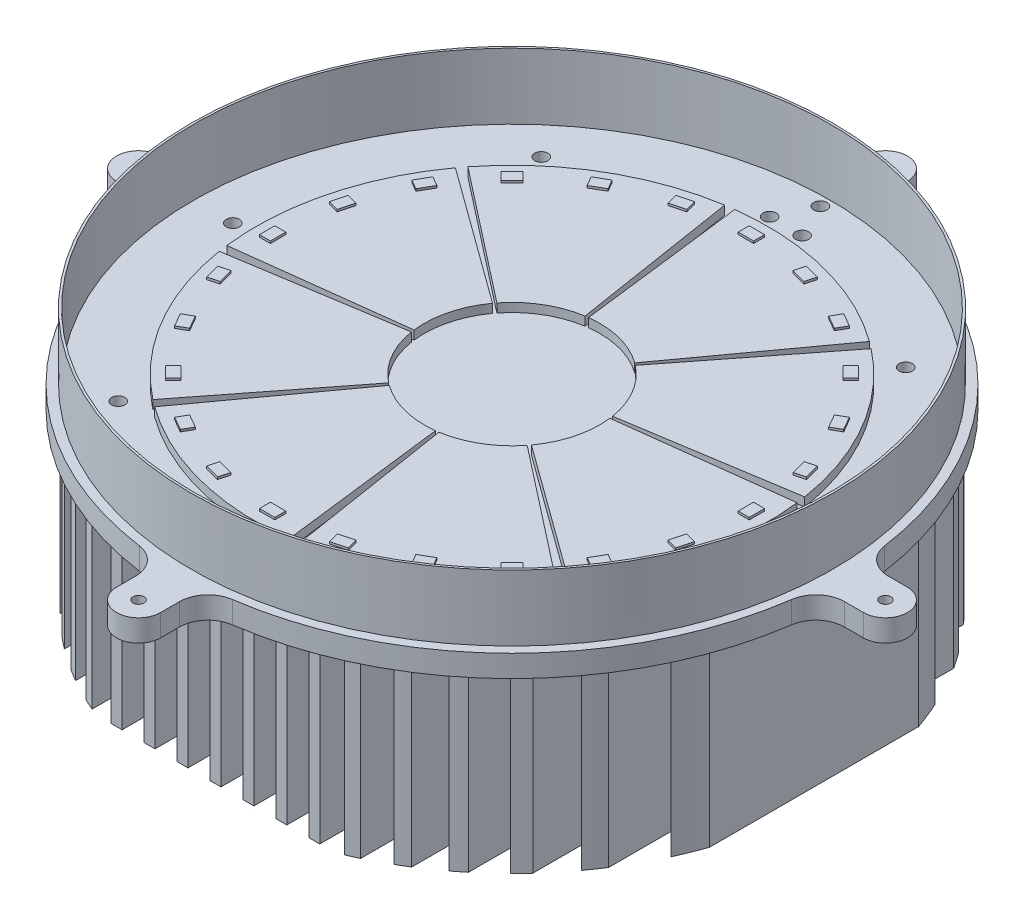
SolidWorks part; units mm, degrees
ref_plane "Front Plane" through (0, 0, 0) normal (0, 0, 1) x (1, 0, 0)
ref_plane "Top Plane" through (0, 0, 0) normal (0, 1, 0) x (1, 0, 0)
ref_plane "Right Plane" through (0, 0, 0) normal (1, 0, 0) x (0, 0, -1)
sketch "Sketch2" plane through (0, 0, 0) normal (0, 1, 0) x (1, 0, 0)
  line L0 (0, 0) -> (0, -224.3017) construction
  line L1 (0, 0) -> (0, 200) construction
  line L2 (0, 0) -> (207.2583, 0) construction
  line L3 (0, 0) -> (-200, 0) construction
  circle A0 centre (0, 0) radius 146
  circle A1 centre (0, 0) radius 145
  point P36 (0, 0)
  dimension "D1" = 290
  dimension "D2" = 292
extrude "Boss-Extrude2" add sketch "Sketch2" along normal blind 30 contours A1 | A0
sketch "Sketch3" plane through (0, 0, 0) normal (0, 1, 0) x (1, 0, 0)
  line L0 (0, 0) -> (211.9111, 0) construction
  line L1 (0, 0) -> (-205.2426, 0) construction
  line L2 (0, 0) -> (0, 170) construction
  line L3 (0, 0) -> (0, -200) construction
  line L4 (161.3691, 10) -> (170, 10)
  line L5 (161.3691, -10) -> (170, -10)
  line L6 (-10, 161.3691) -> (-10, 170)
  line L7 (10, 161.3691) -> (10, 170)
  line L8 (10, -161.3691) -> (10, -170)
  line L9 (-10, -161.3691) -> (-10, -170)
  line L10 (-161.3691, -10) -> (-170, -10)
  line L11 (-161.3691, 10) -> (-170, 10)
  arc A0 (-21.1656, 148.4992) -> (-148.4992, 21.1656) centre (0, 0) ccw
  circle A1 centre (0, 170) radius 2.5
  arc A2 (-10, 170) -> (10, 170) centre (0, 170) cw
  arc A3 (10, 161.3691) -> (21.1656, 148.4992) centre (23, 161.3691) ccw
  arc A4 (-10, 161.3691) -> (-21.1656, 148.4992) centre (-23, 161.3691) cw
  arc A5 (170, 10) -> (170, -10) centre (170, 0) cw
  arc A6 (161.3691, 10) -> (148.4992, 21.1656) centre (161.3691, 23) cw
  circle A7 centre (170, 0) radius 2.5
  arc A8 (161.3691, -10) -> (148.4992, -21.1656) centre (161.3691, -23) ccw
  arc A9 (10, -170) -> (-10, -170) centre (0, -170) cw
  arc A10 (10, -161.3691) -> (21.1656, -148.4992) centre (23, -161.3691) cw
  circle A11 centre (0, -170) radius 2.5
  arc A12 (-10, -161.3691) -> (-21.1656, -148.4992) centre (-23, -161.3691) ccw
  arc A13 (-170, -10) -> (-170, 10) centre (-170, 0) cw
  arc A14 (-161.3691, -10) -> (-148.4992, -21.1656) centre (-161.3691, -23) cw
  circle A15 centre (-170, 0) radius 2.5
  arc A16 (-161.3691, 10) -> (-148.4992, 21.1656) centre (-161.3691, 23) ccw
  arc A17 (-148.4992, -21.1656) -> (-21.1656, -148.4992) centre (0, 0) ccw
  arc A18 (148.4992, 21.1656) -> (21.1656, 148.4992) centre (0, 0) ccw
  arc A19 (21.1656, -148.4992) -> (148.4992, -21.1656) centre (0, 0) ccw
  point P53 (0, 0)
  dimension "D1" = 300
  dimension "D4" = 5
  dimension "D2" = 4
extrude "Boss-Extrude4" add sketch "Sketch3" against normal blind 10
sketch "Sketch4" plane through (0, -10, 0) normal (0, -1, 0) x (1, 0, 0)
  line L0 (0, 0) -> (0, -192.7937) construction
  line L1 (0, 0) -> (0, 216.5128) construction
  line L2 (0, 0) -> (-235.9747, 0) construction
  line L3 (0, 0) -> (242.3846, 0) construction
  line L4 (2.5, -135) -> (-2.5, -135)
  line L5 (2.5, 135) -> (-2.5, 135)
  line L6 (-2.5, -135) -> (-2.5, 135)
  line L7 (2.5, -135) -> (2.5, 135)
  line L8 (12.5, -135) -> (12.5, 135)
  line L9 (17.5, -135) -> (12.5, -135)
  line L10 (17.5, -135) -> (17.5, 135)
  line L11 (17.5, 135) -> (12.5, 135)
  line L12 (27.5, -135) -> (27.5, 135)
  line L13 (32.5, -135) -> (27.5, -135)
  line L14 (32.5, -135) -> (32.5, 135)
  line L15 (32.5, 135) -> (27.5, 135)
  line L16 (42.5, -135) -> (42.5, 135)
  line L17 (47.5, -135) -> (42.5, -135)
  line L18 (47.5, -135) -> (47.5, 135)
  line L19 (47.5, 135) -> (42.5, 135)
  line L20 (57.5, -133.6563) -> (57.5, 133.6563)
  line L22 (62.5, -131.3925) -> (62.5, 131.3925)
  line L24 (72.5, -126.1507) -> (72.5, 126.1507)
  line L26 (77.5, -123.1422) -> (77.5, 123.1422)
  line L28 (87.5, -116.2497) -> (87.5, 116.2497)
  line L30 (92.5, -112.3121) -> (92.5, 112.3121)
  line L32 (102.5, -103.2666) -> (102.5, 103.2666)
  line L34 (107.5, -98.051) -> (107.5, 98.051)
  line L36 (117.5, -85.8138) -> (117.5, 85.8138)
  line L38 (122.5, -78.5111) -> (122.5, 78.5111)
  line L40 (132.5, -60.1166) -> (132.5, 60.1166)
  line L42 (137.5, -47.5815) -> (137.5, 47.5815)
  line L44 (-12.5, -135) -> (-17.5, -135)
  line L45 (-12.5, -135) -> (-12.5, 135)
  line L46 (-17.5, -135) -> (-17.5, 135)
  line L47 (-12.5, 135) -> (-17.5, 135)
  line L48 (-27.5, -135) -> (-32.5, -135)
  line L49 (-27.5, -135) -> (-27.5, 135)
  line L50 (-32.5, -135) -> (-32.5, 135)
  line L51 (-27.5, 135) -> (-32.5, 135)
  line L52 (-42.5, -135) -> (-47.5, -135)
  line L53 (-42.5, -135) -> (-42.5, 135)
  line L54 (-47.5, -135) -> (-47.5, 135)
  line L55 (-42.5, 135) -> (-47.5, 135)
  line L57 (-57.5, -133.6563) -> (-57.5, 133.6563)
  line L58 (-62.5, -131.3925) -> (-62.5, 131.3925)
  line L61 (-72.5, -126.1507) -> (-72.5, 126.1507)
  line L62 (-77.5, -123.1422) -> (-77.5, 123.1422)
  line L65 (-87.5, -116.2497) -> (-87.5, 116.2497)
  line L66 (-92.5, -112.3121) -> (-92.5, 112.3121)
  line L69 (-102.5, -103.2666) -> (-102.5, 103.2666)
  line L70 (-107.5, -98.051) -> (-107.5, 98.051)
  line L73 (-117.5, -85.8138) -> (-117.5, 85.8138)
  line L74 (-122.5, -78.5111) -> (-122.5, 78.5111)
  line L77 (-132.5, -60.1166) -> (-132.5, 60.1166)
  line L78 (-137.5, -47.5815) -> (-137.5, 47.5815)
  line L80 (2.5, -135) -> (-12.5, -135) construction
  line L81 (62.5, 135) -> (57.5, 135) [skipped]
  line L82 (77.5, 135) -> (72.5, 135) [skipped]
  line L83 (92.5, 135) -> (87.5, 135) [skipped]
  line L84 (107.5, 135) -> (102.5, 135) [skipped]
  line L85 (137.5, 135) -> (132.5, 135) [skipped]
  line L86 (122.5, 135) -> (117.5, 135) [skipped]
  line L87 (-57.5, 135) -> (-62.5, 135) [skipped]
  line L88 (-72.5, 135) -> (-77.5, 135) [skipped]
  line L89 (-87.5, 135) -> (-92.5, 135) [skipped]
  line L90 (-102.5, 135) -> (-107.5, 135) [skipped]
  line L91 (-117.5, 135) -> (-122.5, 135) [skipped]
  line L92 (-132.5, 135) -> (-137.5, 135) [skipped]
  line L93 (-57.5, -135) -> (-62.5, -135) [skipped]
  line L94 (62.5, -135) -> (57.5, -135) [skipped]
  line L95 (77.5, -135) -> (72.5, -135) [skipped]
  line L96 (137.5, -135) -> (132.5, -135) [skipped]
  line L97 (122.5, -135) -> (117.5, -135) [skipped]
  line L98 (107.5, -135) -> (102.5, -135) [skipped]
  line L99 (92.5, -135) -> (87.5, -135) [skipped]
  line L100 (-132.5, -135) -> (-137.5, -135) [skipped]
  line L101 (-117.5, -135) -> (-122.5, -135) [skipped]
  line L102 (-102.5, -135) -> (-107.5, -135) [skipped]
  line L103 (-87.5, -135) -> (-92.5, -135) [skipped]
  line L104 (-72.5, -135) -> (-77.5, -135) [skipped]
  arc A2 (132.5, -60.1166) -> (137.5, -47.5815) centre (0, 0) ccw
  arc A3 (117.5, -85.8138) -> (122.5, -78.5111) centre (0, 0) ccw
  arc A4 (102.5, -103.2666) -> (107.5, -98.051) centre (0, 0) ccw
  arc A5 (87.5, -116.2497) -> (92.5, -112.3121) centre (0, 0) ccw
  arc A6 (72.5, -126.1507) -> (77.5, -123.1422) centre (0, 0) ccw
  arc A7 (57.5, -133.6563) -> (62.5, -131.3925) centre (0, 0) ccw
  arc A8 (-77.5, -123.1422) -> (-72.5, -126.1507) centre (0, 0) ccw
  arc A9 (-62.5, -131.3925) -> (-57.5, -133.6563) centre (0, 0) ccw
  arc A10 (-92.5, -112.3121) -> (-87.5, -116.2497) centre (0, 0) ccw
  arc A11 (-107.5, -98.051) -> (-102.5, -103.2666) centre (0, 0) ccw
  arc A12 (-122.5, -78.5111) -> (-117.5, -85.8138) centre (0, 0) ccw
  arc A13 (-137.5, -47.5815) -> (-132.5, -60.1166) centre (0, 0) ccw
  arc A14 (137.5, 47.5815) -> (132.5, 60.1166) centre (0, 0) ccw
  arc A15 (122.5, 78.5111) -> (117.5, 85.8138) centre (0, 0) ccw
  arc A16 (107.5, 98.051) -> (102.5, 103.2666) centre (0, 0) ccw
  arc A17 (92.5, 112.3121) -> (87.5, 116.2497) centre (0, 0) ccw
  arc A18 (77.5, 123.1422) -> (72.5, 126.1507) centre (0, 0) ccw
  arc A19 (62.5, 131.3925) -> (57.5, 133.6563) centre (0, 0) ccw
  arc A20 (-57.5, 133.6563) -> (-62.5, 131.3925) centre (0, 0) ccw
  arc A21 (-72.5, 126.1507) -> (-77.5, 123.1422) centre (0, 0) ccw
  arc A22 (-87.5, 116.2497) -> (-92.5, 112.3121) centre (0, 0) ccw
  arc A23 (-102.5, 103.2666) -> (-107.5, 98.051) centre (0, 0) ccw
  arc A24 (-117.5, 85.8138) -> (-122.5, 78.5111) centre (0, 0) ccw
  arc A25 (-132.5, 60.1166) -> (-137.5, 47.5815) centre (0, 0) ccw
  dimension "D5" = 291
  dimension "D1" = 135
  dimension "D2" = 2.5
  dimension "D4" = 15
  dimension "D3" = 10
extrude "Boss-Extrude5" add sketch "Sketch4" along normal blind 80
sketch "Sketch8" plane through (0, 0, 0) normal (0, 1, 0) x (1, 0, 0)
  line L8 (4.8748, -39.7018) -> (14.1944, -115.6039)
  line L9 (-24.6265, -31.5204) -> (-71.7074, -91.7813)
  line L10 (-39.7018, -4.8748) -> (-115.6039, -14.1944)
  line L11 (-31.5204, 24.6265) -> (-91.7813, 71.7074)
  line L12 (-4.8748, 39.7018) -> (-14.1944, 115.6039)
  line L13 (24.6265, 31.5204) -> (71.7074, 91.7813)
  line L14 (39.7018, 4.8748) -> (115.6039, 14.1944)
  line L15 (31.5204, -24.6265) -> (91.7813, -71.7074)
  line L16 (6.2574, -39.5075) -> (18.2202, -115.0381)
  line L17 (32.3607, -23.5114) -> (94.2279, -68.4606)
  line L18 (39.5075, 6.2574) -> (115.0381, 18.2202)
  line L19 (23.5114, 32.3607) -> (68.4606, 94.2279)
  line L20 (-6.2574, 39.5075) -> (-18.2202, 115.0381)
  line L21 (-32.3607, 23.5114) -> (-94.2279, 68.4606)
  line L22 (-39.5075, -6.2574) -> (-115.0381, -18.2202)
  line L23 (-23.5114, -32.3607) -> (-68.4606, -94.2279)
  arc A0 (115.0381, 18.2202) -> (71.7074, 91.7813) centre (0, 0) ccw
  arc A1 (32.3607, -23.5114) -> (39.7018, 4.8748) centre (0, 0) ccw
  arc A2 (6.2574, -39.5075) -> (31.5204, -24.6265) centre (0, 0) ccw
  arc A3 (-23.5114, -32.3607) -> (4.8748, -39.7018) centre (0, 0) ccw
  arc A4 (-39.5075, -6.2574) -> (-24.6265, -31.5204) centre (0, 0) ccw
  arc A5 (-32.3607, 23.5114) -> (-39.7018, -4.8748) centre (0, 0) ccw
  arc A6 (-6.2574, 39.5075) -> (-31.5204, 24.6265) centre (0, 0) ccw
  arc A7 (23.5114, 32.3607) -> (-4.8748, 39.7018) centre (0, 0) ccw
  arc A8 (39.5075, 6.2574) -> (24.6265, 31.5204) centre (0, 0) ccw
  arc A9 (94.2279, -68.4606) -> (115.6039, 14.1944) centre (0, 0) ccw
  arc A10 (18.2202, -115.0381) -> (91.7813, -71.7074) centre (0, 0) ccw
  arc A11 (-68.4606, -94.2279) -> (14.1944, -115.6039) centre (0, 0) ccw
  arc A12 (-115.0381, -18.2202) -> (-71.7074, -91.7813) centre (0, 0) ccw
  arc A13 (-94.2279, 68.4606) -> (-115.6039, -14.1944) centre (0, 0) ccw
  arc A14 (-18.2202, 115.0381) -> (-91.7813, 71.7074) centre (0, 0) ccw
  arc A15 (68.4606, 94.2279) -> (-14.1944, 115.6039) centre (0, 0) ccw
  point P15 (0, 0)
  point P22 (0, 0)
  dimension "D2" = 8
extrude "Boss-Extrude7" add sketch "Sketch8" along normal blind 4
sketch "Sketch5" plane through (0, 4, 0) normal (0, 1, 0) x (1, 0, 0)
  line L0 (0, 0) -> (233.0388, 0) construction
  line L1 (0, 0) -> (-266.1331, 0) construction
  line L2 (0, 0) -> (0, 192.8201) construction
  line L3 (0, 0) -> (0, -200.634) construction
  line L4 (0, 111.4786) -> (3.5, 111.4786)
  line L5 (0, 111.4786) -> (-3.5, 111.4786)
  line L6 (3.5, 106.4786) -> (3.5, 111.4786)
  line L7 (-3.5, 106.4786) -> (-3.5, 111.4786)
  line L8 (0, 106.4786) -> (3.5, 106.4786)
  line L9 (0, 106.4786) -> (-3.5, 106.4786)
  line L10 (24.1779, 103.7563) -> (25.472, 108.5859)
  line L11 (28.8528, 107.68) -> (25.472, 108.5859)
  line L12 (28.8528, 107.68) -> (32.2335, 106.7742)
  line L13 (30.9394, 101.9445) -> (32.2335, 106.7742)
  line L14 (27.5587, 102.8504) -> (30.9394, 101.9445)
  line L15 (27.5587, 102.8504) -> (24.1779, 103.7563)
  line L16 (50.2082, 93.9631) -> (52.7082, 98.2933)
  line L17 (55.7393, 96.5433) -> (52.7082, 98.2933)
  line L18 (55.7393, 96.5433) -> (58.7704, 94.7933)
  line L19 (56.2704, 90.4631) -> (58.7704, 94.7933)
  line L20 (53.2393, 92.2131) -> (56.2704, 90.4631)
  line L21 (53.2393, 92.2131) -> (50.2082, 93.9631)
  line L22 (72.8168, 77.7666) -> (76.3524, 81.3021)
  line L23 (78.8273, 78.8273) -> (76.3524, 81.3021)
  line L24 (78.8273, 78.8273) -> (81.3021, 76.3524)
  line L25 (77.7666, 72.8168) -> (81.3021, 76.3524)
  line L26 (75.2917, 75.2917) -> (77.7666, 72.8168)
  line L27 (75.2917, 75.2917) -> (72.8168, 77.7666)
  line L28 (90.4631, 56.2704) -> (94.7933, 58.7704)
  line L29 (96.5433, 55.7393) -> (94.7933, 58.7704)
  line L30 (96.5433, 55.7393) -> (98.2933, 52.7082)
  line L31 (93.9631, 50.2082) -> (98.2933, 52.7082)
  line L32 (92.2131, 53.2393) -> (93.9631, 50.2082)
  line L33 (92.2131, 53.2393) -> (90.4631, 56.2704)
  line L34 (101.9445, 30.9394) -> (106.7742, 32.2335)
  line L35 (107.68, 28.8528) -> (106.7742, 32.2335)
  line L36 (107.68, 28.8528) -> (108.5859, 25.472)
  line L37 (103.7563, 24.1779) -> (108.5859, 25.472)
  line L38 (102.8504, 27.5587) -> (103.7563, 24.1779)
  line L39 (102.8504, 27.5587) -> (101.9445, 30.9394)
  line L40 (106.4786, 3.5) -> (111.4786, 3.5)
  line L41 (111.4786, 0) -> (111.4786, 3.5)
  line L42 (111.4786, 0) -> (111.4786, -3.5)
  line L43 (106.4786, -3.5) -> (111.4786, -3.5)
  line L44 (106.4786, 0) -> (106.4786, -3.5)
  line L45 (106.4786, 0) -> (106.4786, 3.5)
  line L46 (103.7563, -24.1779) -> (108.5859, -25.472)
  line L47 (107.68, -28.8528) -> (108.5859, -25.472)
  line L48 (107.68, -28.8528) -> (106.7742, -32.2335)
  line L49 (101.9445, -30.9394) -> (106.7742, -32.2335)
  line L50 (102.8504, -27.5587) -> (101.9445, -30.9394)
  line L51 (102.8504, -27.5587) -> (103.7563, -24.1779)
  line L52 (93.9631, -50.2082) -> (98.2933, -52.7082)
  line L53 (96.5433, -55.7393) -> (98.2933, -52.7082)
  line L54 (96.5433, -55.7393) -> (94.7933, -58.7704)
  line L55 (90.4631, -56.2704) -> (94.7933, -58.7704)
  line L56 (92.2131, -53.2393) -> (90.4631, -56.2704)
  line L57 (92.2131, -53.2393) -> (93.9631, -50.2082)
  line L58 (77.7666, -72.8168) -> (81.3021, -76.3524)
  line L59 (78.8273, -78.8273) -> (81.3021, -76.3524)
  line L60 (78.8273, -78.8273) -> (76.3524, -81.3021)
  line L61 (72.8168, -77.7666) -> (76.3524, -81.3021)
  line L62 (75.2917, -75.2917) -> (72.8168, -77.7666)
  line L63 (75.2917, -75.2917) -> (77.7666, -72.8168)
  line L64 (56.2704, -90.4631) -> (58.7704, -94.7933)
  line L65 (55.7393, -96.5433) -> (58.7704, -94.7933)
  line L66 (55.7393, -96.5433) -> (52.7082, -98.2933)
  line L67 (50.2082, -93.9631) -> (52.7082, -98.2933)
  line L68 (53.2393, -92.2131) -> (50.2082, -93.9631)
  line L69 (53.2393, -92.2131) -> (56.2704, -90.4631)
  line L70 (30.9394, -101.9445) -> (32.2335, -106.7742)
  line L71 (28.8528, -107.68) -> (32.2335, -106.7742)
  line L72 (28.8528, -107.68) -> (25.472, -108.5859)
  line L73 (24.1779, -103.7563) -> (25.472, -108.5859)
  line L74 (27.5587, -102.8504) -> (24.1779, -103.7563)
  line L75 (27.5587, -102.8504) -> (30.9394, -101.9445)
  line L76 (3.5, -106.4786) -> (3.5, -111.4786)
  line L77 (0, -111.4786) -> (3.5, -111.4786)
  line L78 (0, -111.4786) -> (-3.5, -111.4786)
  line L79 (-3.5, -106.4786) -> (-3.5, -111.4786)
  line L80 (0, -106.4786) -> (-3.5, -106.4786)
  line L81 (0, -106.4786) -> (3.5, -106.4786)
  line L82 (-24.1779, -103.7563) -> (-25.472, -108.5859)
  line L83 (-28.8528, -107.68) -> (-25.472, -108.5859)
  line L84 (-28.8528, -107.68) -> (-32.2335, -106.7742)
  line L85 (-30.9394, -101.9445) -> (-32.2335, -106.7742)
  line L86 (-27.5587, -102.8504) -> (-30.9394, -101.9445)
  line L87 (-27.5587, -102.8504) -> (-24.1779, -103.7563)
  line L88 (-50.2082, -93.9631) -> (-52.7082, -98.2933)
  line L89 (-55.7393, -96.5433) -> (-52.7082, -98.2933)
  line L90 (-55.7393, -96.5433) -> (-58.7704, -94.7933)
  line L91 (-56.2704, -90.4631) -> (-58.7704, -94.7933)
  line L92 (-53.2393, -92.2131) -> (-56.2704, -90.4631)
  line L93 (-53.2393, -92.2131) -> (-50.2082, -93.9631)
  line L94 (-72.8168, -77.7666) -> (-76.3524, -81.3021)
  line L95 (-78.8273, -78.8273) -> (-76.3524, -81.3021)
  line L96 (-78.8273, -78.8273) -> (-81.3021, -76.3524)
  line L97 (-77.7666, -72.8168) -> (-81.3021, -76.3524)
  line L98 (-75.2917, -75.2917) -> (-77.7666, -72.8168)
  line L99 (-75.2917, -75.2917) -> (-72.8168, -77.7666)
  line L100 (-90.4631, -56.2704) -> (-94.7933, -58.7704)
  line L101 (-96.5433, -55.7393) -> (-94.7933, -58.7704)
  line L102 (-96.5433, -55.7393) -> (-98.2933, -52.7082)
  line L103 (-93.9631, -50.2082) -> (-98.2933, -52.7082)
  line L104 (-92.2131, -53.2393) -> (-93.9631, -50.2082)
  line L105 (-92.2131, -53.2393) -> (-90.4631, -56.2704)
  line L106 (-101.9445, -30.9394) -> (-106.7742, -32.2335)
  line L107 (-107.68, -28.8528) -> (-106.7742, -32.2335)
  line L108 (-107.68, -28.8528) -> (-108.5859, -25.472)
  line L109 (-103.7563, -24.1779) -> (-108.5859, -25.472)
  line L110 (-102.8504, -27.5587) -> (-103.7563, -24.1779)
  line L111 (-102.8504, -27.5587) -> (-101.9445, -30.9394)
  line L112 (-106.4786, -3.5) -> (-111.4786, -3.5)
  line L113 (-111.4786, 0) -> (-111.4786, -3.5)
  line L114 (-111.4786, 0) -> (-111.4786, 3.5)
  line L115 (-106.4786, 3.5) -> (-111.4786, 3.5)
  line L116 (-106.4786, 0) -> (-106.4786, 3.5)
  line L117 (-106.4786, 0) -> (-106.4786, -3.5)
  line L118 (-103.7563, 24.1779) -> (-108.5859, 25.472)
  line L119 (-107.68, 28.8528) -> (-108.5859, 25.472)
  line L120 (-107.68, 28.8528) -> (-106.7742, 32.2335)
  line L121 (-101.9445, 30.9394) -> (-106.7742, 32.2335)
  line L122 (-102.8504, 27.5587) -> (-101.9445, 30.9394)
  line L123 (-102.8504, 27.5587) -> (-103.7563, 24.1779)
  line L124 (-93.9631, 50.2082) -> (-98.2933, 52.7082)
  line L125 (-96.5433, 55.7393) -> (-98.2933, 52.7082)
  line L126 (-96.5433, 55.7393) -> (-94.7933, 58.7704)
  line L127 (-90.4631, 56.2704) -> (-94.7933, 58.7704)
  line L128 (-92.2131, 53.2393) -> (-90.4631, 56.2704)
  line L129 (-92.2131, 53.2393) -> (-93.9631, 50.2082)
  line L130 (-77.7666, 72.8168) -> (-81.3021, 76.3524)
  line L131 (-78.8273, 78.8273) -> (-81.3021, 76.3524)
  line L132 (-78.8273, 78.8273) -> (-76.3524, 81.3021)
  line L133 (-72.8168, 77.7666) -> (-76.3524, 81.3021)
  line L134 (-75.2917, 75.2917) -> (-72.8168, 77.7666)
  line L135 (-75.2917, 75.2917) -> (-77.7666, 72.8168)
  line L136 (-56.2704, 90.4631) -> (-58.7704, 94.7933)
  line L137 (-55.7393, 96.5433) -> (-58.7704, 94.7933)
  line L138 (-55.7393, 96.5433) -> (-52.7082, 98.2933)
  line L139 (-50.2082, 93.9631) -> (-52.7082, 98.2933)
  line L140 (-53.2393, 92.2131) -> (-50.2082, 93.9631)
  line L141 (-53.2393, 92.2131) -> (-56.2704, 90.4631)
  line L142 (-30.9394, 101.9445) -> (-32.2335, 106.7742)
  line L143 (-28.8528, 107.68) -> (-32.2335, 106.7742)
  line L144 (-28.8528, 107.68) -> (-25.472, 108.5859)
  line L145 (-24.1779, 103.7563) -> (-25.472, 108.5859)
  line L146 (-27.5587, 102.8504) -> (-24.1779, 103.7563)
  line L147 (-27.5587, 102.8504) -> (-30.9394, 101.9445)
  point P33 (0, 0)
  dimension "D1" = 3.5
  dimension "D2" = 5
  dimension "D3" = 24
extrude "Boss-Extrude6" add sketch "Sketch5" along normal blind 1
sketch "Sketch7" plane through (0, 0, 0) normal (0, 1, 0) x (1, 0, 0)
  line L0 (0, 0) -> (0, 199.2983) construction
  line L1 (180, 0) -> (-209.1437, 0) construction
  line L2 (0, 0) -> (0, -219.846) construction
  arc A0 (170, -10) -> (170, 10) centre (170, 0) ccw construction
  circle A1 centre (-127.0882, 0) radius 3
  circle A2 centre (0, 140.3779) radius 3
  circle A3 centre (0, -140.3779) radius 3
  circle A4 centre (127.0882, 0) radius 3
  circle A5 centre (-67.7124, 0) radius 3
  circle A6 centre (-52.1309, 49.6625) radius 3
  circle A7 centre (52.1309, 49.6625) radius 3
  circle A8 centre (52.1309, -49.6625) radius 3
  circle A9 centre (-52.1309, -49.6625) radius 3
  circle A10 centre (67.7124, 0) radius 3
  circle A11 centre (-82.9543, 96.2809) radius 3
  circle A12 centre (82.9543, 96.2809) radius 3
  circle A13 centre (82.9543, -96.2809) radius 3
  circle A14 centre (-82.9543, -96.2809) radius 3
  circle A15 centre (7.3999, -124.6624) radius 3
  circle A16 centre (-7.3999, -124.6624) radius 3
  circle A17 centre (7.3999, 124.6624) radius 3
  circle A18 centre (-7.3999, 124.6624) radius 3
  dimension "D2" = 6
extrude "Cut-Extrude1" cut sketch "Sketch7" against normal blind 10
